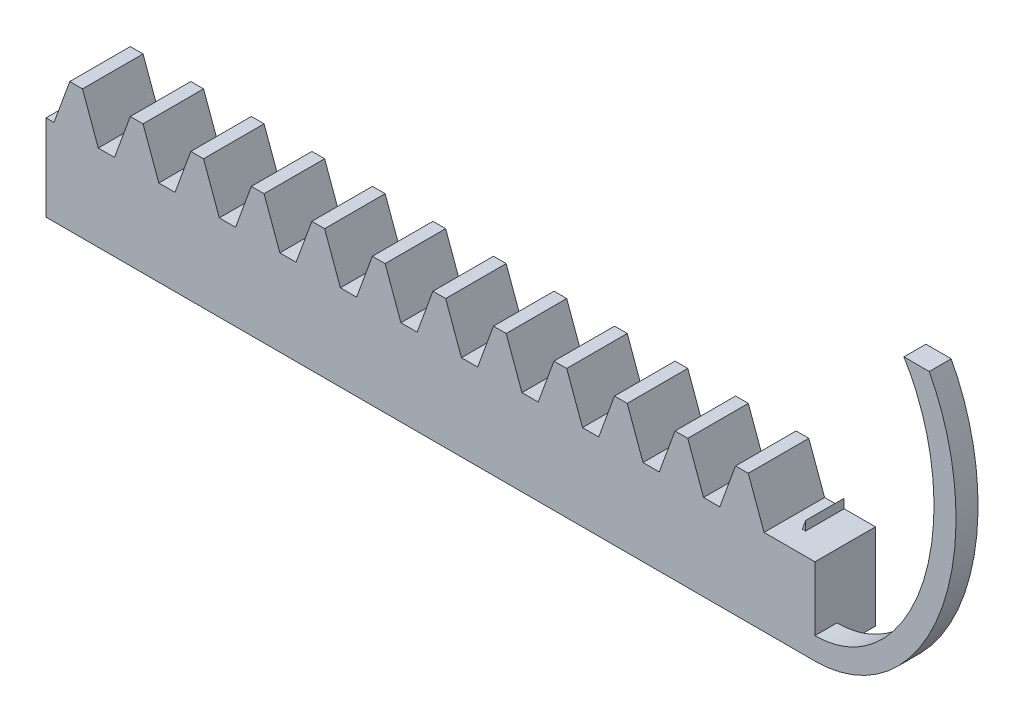
SolidWorks part; units mm, degrees
extrude "Blank" add sketch "BlankSke" against normal blind 10
sketch "BlankSke" plane through (0, 0, 0) normal (0, 0, 1) x (1, 0, 0)
  line L1 (0, 0) -> (100, 0)
  line L2 (0, 0) -> (0, 11.75)
  line L3 (0, 11.75) -> (100, 11.75)
  line L4 (100, 0) -> (100, 11.75)
  dimension "Length" = 100
  dimension "Blank_height" = 11.75
ref_plane "Plane1" through (0, 0, 0) normal (0, 0, 1) x (1, 0, 0)
ref_plane "Plane2" through (0, 0, 0) normal (0, 1, 0) x (1, 0, 0)
ref_plane "Plane3" through (0, 0, 0) normal (1, 0, 0) x (0, 0, -1)
other "Configuration Table"
sketch "HoldingSke" plane through (0, 0, 0) normal (0, 1, 0) x (1, 0, 0)
  line L0 (0, 0) -> (0.0795, 0.5659)
  line L1 (-15, 0) -> (100, 0) construction
  line L2 (0, 0) -> (-2.1039, 2.3779)
  line L3 (0, 0) -> (-11.863, 4.5341)
  line L4 (0, 0) -> (8.1152, 2.9537)
  line L5 (0, 0) -> (-23.7986, -8.8762)
  line L6 (0, 0) -> (-10.5278, -7.1032)
  line L9 (-71.009, 38.7566) -> (22.9603, 72.9586)
  line L10 (-76.2, 4.1279) -> (-66.2, 4.1279)
  line L11 (0, 0) -> (-10, 0)
  line L12 (-76.2, 101.6) -> (-76.147, 101.6)
  line L13 (24.9733, 27.94) -> (52.9518, 28.4284)
  line L14 (24.9733, 27.94) -> (24.9743, 27.94)
  line L15 (24.9733, 27.94) -> (100.4006, 29.5858)
  circle A0 centre (0, 0) radius 19.05
  circle A1 centre (0, 0) radius 5
  circle A2 centre (0, 0) radius 12.7
  dimension "MPH" = 10
  dimension "Diameter" = 38.1
  dimension "Num_teeth" = 20
  dimension "Pitch" = 0.5714
  dimension "Show_teeth" = 998
  dimension "Thickness" = 12.7
  dimension "Ap" = 20
  dimension "Pitch_height" = 10
  dimension "Width" = 10
  dimension "Backlash" = 0.053
  dimension "Addendum_fac" = 1
  dimension "Dedendum_fac" = 1.25
  dimension "Clearance_fac" = 0.25
  dimension "Dedendum_add" = 0.001
  dimension "Length" = 100
  dimension "Module" = 1.75
sketch "TooCutSkeIll" plane through (0, 0, 0) normal (0, 0, 1) x (1, 0, 0)
  line L0 (-2.1536, 11.7039) -> (-0.8423, 8.101)
  line L1 (-0.4302, 7.8125) -> (0.4302, 7.8125)
  line L2 (0.8423, 8.101) -> (2.1536, 11.7039)
  line L3 (100, 11.75) -> (0, 11.75) construction
  line L4 (0, 0) -> (0, 64.897) construction
  line L5 (-13.208, 10) -> (12.954, 10) construction
  line L6 (0, 0) -> (100, 0) construction
  line L7 (1.5334, 10) -> (1.5334, 48.7463) construction
  line L8 (-1.5334, 10) -> (-1.5334, 48.7463) construction
  line L9 (2.2194, 11.75) -> (2.2194, 11.7754)
  line L10 (-2.2194, 11.75) -> (-2.2194, 11.7754)
  line L11 (-2.2194, 11.7754) -> (2.2194, 11.7754)
  arc A0 (0.4302, 7.8125) -> (0.8423, 8.101) centre (0.4302, 8.251) ccw
  arc A1 (-0.8423, 8.101) -> (-0.4302, 7.8125) centre (-0.4302, 8.251) ccw
  arc A2 (2.2194, 11.75) -> (2.1536, 11.7039) centre (2.2194, 11.68) ccw
  arc A3 (-2.1536, 11.7039) -> (-2.2194, 11.75) centre (-2.2194, 11.68) ccw
  dimension "Pitch_height" = 10
  dimension "Addendum_plus" = 1.7754
  dimension "Pressure_angle" = 20
  dimension "Gap_width" = 3.0669
  dimension "Dedendum" = 2.1875
extrude "ToothCutIll" [suppressed] cut sketch "TooCutSkeIll" against normal through all
sketch "TooCutSkeSim" plane through (0, 0, 0) normal (0, 0, 1) x (1, 0, 0)
  line L0 (0.7373, 7.8125) -> (-0.7373, 7.8125)
  line L1 (2.1796, 11.7754) -> (0.7373, 7.8125)
  line L2 (0, 17.4625) -> (0, 53.467) construction
  line L3 (2.1796, 11.7754) -> (-2.1796, 11.7754)
  line L6 (-2.1796, 11.7754) -> (-0.7373, 7.8125)
  line L9 (-1.5334, 10) -> (1.5334, 10) construction
  line L10 (0, 0) -> (100, 0) construction
  line L11 (1.5334, 10) -> (1.5334, 53.467) construction
  line L12 (-1.5334, 10) -> (-1.5334, 53.467) construction
  dimension "Pitch_height" = 10
  dimension "Addendum_plus" = 1.7754
  dimension "Pressure_angle" = 20
  dimension "Gap_width" = 3.0669
  dimension "Dedendum" = 2.1875
extrude "ToothCutSim" cut sketch "TooCutSkeSim" against normal through all
pattern_linear "TeethCuts" count 19 spacing 5.4978 along (1, 0, 0) of "ToothCutIll", "ToothCutSim"
sketch "草图3" plane through (0, 0, 0) normal (0, 0, 1) x (1, 0, 0)
  line L0 (100, 0) -> (102.8415, 0)
  line L1 (102.8415, 0) -> (102.8415, 7.8125)
  line L2 (102.8415, 7.8125) -> (100, 7.8125)
  line L3 (100, 7.8125) -> (100, 0)
  line L4 (100, 0) -> (100, 8.6438) construction
  line L5 (98.2229, 7.8125) -> (99.6974, 7.8125) construction
extrude "凸台-拉伸1" add sketch "草图3" against normal up to surface (10 mm away) contours L3 L0 L1 L2 up to face at (50.1593, 9.4613, -10)
sketch "草图5" plane through (0, 0, 0) normal (0, 0, 1) x (1, 0, 0)
  line L0 (102.8415, 0.3026) -> (102.8415, 8.9464) construction
  line L1 (102.8415, 0) -> (102.8415, 2)
  line L2 (102.8415, 35.2664) -> (102.8415, 33.2664)
  arc A0 (102.8415, 0) -> (102.8415, 35.2664) centre (102.8415, 17.6332) ccw construction
  ellipse E0 centre (102.8415, 17.6332) end of major axis (102.8415, 35.2664) minor radius 12.82 (102.8415, 0) -> (102.8415, 35.2664) ccw
  spline S0 degree 1 poles (102.8415, 2) (102.8415, 33.2664) knots 0 0 1 1 construction
  spline S1 degree 3 poles (102.8415, 2) (103.5053, 2) (104.8169, 2.1776) (107.4233, 3.2552) (110.4683, 6.0151) (113.0466, 11.2809) (113.969, 17.6332) (113.0466, 23.9855) (110.4683, 29.2513) (107.4233, 32.0112) (104.8169, 33.0888) (103.5053, 33.2664) (102.8415, 33.2664) knots 3.141593 3.141593 3.141593 3.141593 3.337942 3.534292 3.926991 4.31969 4.712389 5.105088 5.497787 5.890486 6.086836 6.283185 6.283185 6.283185 6.283185
  dimension "D1" = 2
extrude "凸台-拉伸2" add sketch "草图5" against normal blind 2 contours L2 S1 L1 E0
sketch "草图6" plane through (0, 0, -10) normal (0, 0, -1) x (-1, 0, 0)
  line L1 (-102.8415, 0) -> (0, 0)
  line L2 (-102.8415, 0) -> (-102.8415, 15)
  line L3 (-102.8415, 15) -> (0, 15)
  line L4 (0, 0) -> (0, 15)
  dimension "D1" = 15
extrude "切除-拉伸2" cut sketch "草图6" against normal blind 4.5 contours L2 L1 L4 L3
sketch "草图7" plane through (0, 0, 0) normal (0, 0, 1) x (1, 0, 0)
  line L0 (102.8415, 7.8125) -> (100, 7.8125) construction
  line L1 (99.3518, 9.0173) -> (100.512, 9.0173)
  line L2 (99.3518, 9.0173) -> (99.3518, 7.8125)
  line L3 (99.3518, 7.8125) -> (100.512, 7.8125)
  line L4 (100.512, 9.0173) -> (100.512, 7.8125)
extrude "切除-拉伸3" cut sketch "草图7" against normal up to surface (2 mm away) up to face at (102.8415, 9.0666, -2)
sketch "草图8" plane through (0, 0, 0) normal (-1, 0, 0) x (0, 0, 1)
  line L1 (8.3331, -13.325) -> (-8.3331, -13.325)
  line L2 (8.3331, -13.325) -> (8.3331, 13.325)
  line L3 (8.3331, 13.325) -> (-8.3331, 13.325)
  line L4 (-8.3331, -13.325) -> (-8.3331, 13.325)
  line L5 (8.3331, -13.325) -> (-8.3331, 13.325) construction
  line L6 (8.3331, 13.325) -> (-8.3331, -13.325) construction
  point P0 (0, 0)
extrude "切除-拉伸5" cut sketch "草图8" against normal blind 33
sketch "草图9" plane through (0, 0, 0) normal (0, 0, 1) x (1, 0, 0)
  ellipse E0 centre (102.8415, 17.6332) end of major axis (102.8415, 35.2664) minor radius 12.82 (102.8415, 0) -> (102.8415, 35.2664) ccw construction
  point P0 (115.6438, 16.7056)
sketch "草图10" plane through (0, 0, 0) normal (0, 0, 1) x (1, 0, 0)
  ellipse E0 centre (102.8415, 17.6332) end of major axis (102.8415, 35.2664) minor radius 12.82 (102.8415, 0) -> (102.8415, 35.2664) ccw construction
  point P0 (115.6328, 16.454)
sketch "草图11" plane through (0, 0, 0) normal (0, 0, 1) x (1, 0, 0)
  line L1 (86.6685, 42.7967) -> (122.2617, 42.7967)
  line L2 (86.6685, 42.7967) -> (86.6685, 27.9736)
  line L3 (86.6685, 27.9736) -> (122.2617, 27.9736)
  line L4 (122.2617, 42.7967) -> (122.2617, 27.9736)
extrude "切除-拉伸6" cut sketch "草图11" against normal up to surface (2 mm away) up to face at (102.8415, 9.0666, -2)
equation "' \"Module@HoldingSke\" = 6.35"
equation "' \"Num_teeth@HoldingSke\" = 12"
equation "' \"Ap@HoldingSke\" =  20"
equation "' \"Ap@HoldingSke\" = 20"
equation "' \"Width@HoldingSke\" = 0.25 * 25.4"
equation "' \"Show_teeth@HoldingSke\" = 500"
equation "' \"Backlash@HoldingSke\" = 0.009 * 25.4"
equation "' \"Addendum_fac@HoldingSke\" = 1.0"
equation "' \"Dedendum_fac@HoldingSke\" = 1.25"
equation "' \"Dedendum_add@HoldingSke\" = 0.00005 * 25.4"
equation "' \"Clearance_fac@HoldingSke\" = 0.25"
equation "' \"Pitch_height@HoldingSke\" = 1 * 25.4"
equation "' \"Length@HoldingSke\" = 4.71 * 25.4"
equation "\"Pitch@HoldingSke\" = 1 / \"Module@HoldingSke\""
equation "\"MPH@HoldingSke\" = \"Dedendum_fac@HoldingSke\" / \"Pitch@HoldingSke\" + 2 * \"Dedendum_add@HoldingSke\" + 0.002 * 25.4"
equation "\"MPH@HoldingSke\" = ((sgn( \"MPH@HoldingSke\" - \"Pitch_height@HoldingSke\")+1)*( \"MPH@HoldingSke\" - \"Pitch_height@HoldingSke\"))/2 + \"Pitch_height@HoldingSke\""
equation "\"Blank_height@BlankSke\" = \"Pitch_height@HoldingSke\" + \"Addendum_fac@HoldingSke\"  / \"Pitch@HoldingSke\" "
equation "\"Length@BlankSke\" =  \"Length@HoldingSke\""
equation "\"Face_width@Blank\" = \"Width@HoldingSke\""
equation "\"Pressure_angle@TooCutSkeIll\" = \"Ap@HoldingSke\""
equation "\"Addendum_plus@TooCutSkeIll\" =  \"Addendum_fac@HoldingSke\"  / \"Pitch@HoldingSke\" + 0.001 *25.4"
equation "\"Dedendum@TooCutSkeIll\" = \"Dedendum_fac@HoldingSke\"  / \"Pitch@HoldingSke\""
equation "\"Pitch_height@TooCutSkeIll\" =  \"MPH@HoldingSke\""
equation "\"Gap_width@TooCutSkeIll\" = 3.14159265 / 2 / \"Pitch@HoldingSke\" + 6 * \"Backlash@HoldingSke\""
equation "\"Pressure_angle@TooCutSkeSim\" = \"Ap@HoldingSke\""
equation "\"Addendum_plus@TooCutSkeSim\" =  \"Addendum_fac@HoldingSke\"  / \"Pitch@HoldingSke\" + 0.001 * 25.4"
equation "\"Dedendum@TooCutSkeSim\" = \"Dedendum_fac@HoldingSke\"  / \"Pitch@HoldingSke\""
equation "\"Pitch_height@TooCutSkeSim\" =  \"MPH@HoldingSke\""
equation "\"Gap_width@TooCutSkeSim\" = 3.14159265 / 2 / \"Pitch@HoldingSke\" + 6 * \"Backlash@HoldingSke\""
equation "\"Root_fillet@TooCutSkeIll\" = \"Clearance_fac@HoldingSke\" / \"Pitch@HoldingSke\" + \"Dedendum_add@HoldingSke\""
equation "\"Break_rad@TooCutSkeIll\" = 0.02 / \"Pitch@HoldingSke\" * 2"
equation "\"Linear_pitch@TeethCuts\" = 3.14159265 / \"Pitch@HoldingSke\""
equation "\"Num_teeth@HoldingSke\" = int( ( \"Length@HoldingSke\" + 0 ) / (3.14159265 / \"Pitch@HoldingSke\")) + 0.9999  + 1"
equation " \"Num_teeth@TeethCuts\" = int( \"Show_teeth@HoldingSke\" ) + 1"
equation " \"Num_teeth@TeethCuts\" = ((sgn( \"Num_teeth@TeethCuts\" - \"Num_teeth@HoldingSke\" )-1)*( \"Num_teeth@TeethCuts\" - \"Num_teeth@HoldingSke\" ))/-2+ \"Num_teeth@HoldingSke\""
equation " \"Num_teeth@TeethCuts\" = ((sgn( \"Num_teeth@TeethCuts\" - 2.0)+1)*( \"Num_teeth@TeethCuts\" - 2.0))/2 +2.0"
